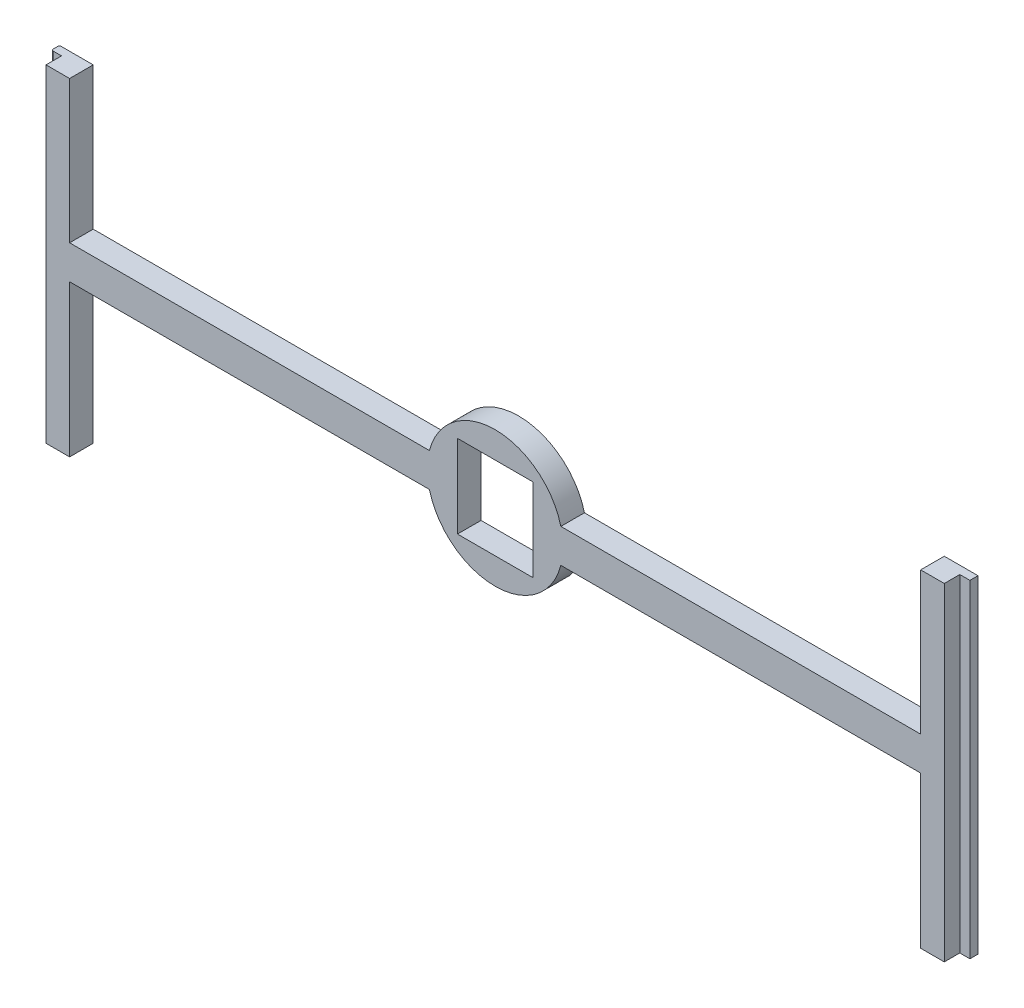
SolidWorks part; units mm, degrees
ref_plane "Front Plane" through (0, 0, 0) normal (0, 0, 1) x (1, 0, 0)
ref_plane "Top Plane" through (0, 0, 0) normal (0, 1, 0) x (1, 0, 0)
ref_plane "Right Plane" through (0, 0, 0) normal (1, 0, 0) x (0, 0, -1)
sketch "Sketch1" plane through (0, 0, 0) normal (0, 0, 1) x (1, 0, 0)
  line L0 (0, 2.5654) -> (0, -2.5654) construction
  line L1 (-63.1, 2.5) -> (-9.7428, 2.5)
  line L3 (-63.1, -2.5) -> (-9.7428, -2.5)
  line L5 (63.1, 25) -> (68.1, 25)
  line L6 (63.1, 25) -> (63.1, 2.5)
  line L7 (63.1, -25) -> (68.1, -25)
  line L8 (68.1, 25) -> (68.1, -25)
  line L9 (-63.1, -25) -> (-68.1, -25)
  line L10 (-68.1, 25) -> (-68.1, -25)
  line L11 (-63.1, 25) -> (-68.1, 25)
  line L12 (-63.1, 25) -> (-63.1, 2.5)
  line L13 (-63.1, -2.5) -> (-63.1, -25)
  line L14 (63.1, -2.5) -> (63.1, -25)
  line L15 (63.1, 2.5) -> (63.1, -2.5) construction
  line L17 (9.7428, 2.5) -> (63.1, 2.5)
  line L18 (9.7428, -2.5) -> (63.1, -2.5)
  circle A5 centre (0, 0) radius 2.54
  arc A6 (-9.7428, -2.5) -> (9.7428, -2.5) centre (0, 0) ccw
  arc A7 (9.7428, 2.5) -> (-9.7428, 2.5) centre (0, 0) ccw
  point P23 (63.1, 0)
  point P24 (0, 0)
  point P25 (-68.1, 0)
  dimension "D5" = 5.08
  dimension "D6" = 20.1168
  dimension "D1" = 126.2
  dimension "D2" = 5
  dimension "D3" = 50
  dimension "D4" = 5
extrude "Boss-Extrude1" add sketch "Sketch1" along normal blind 3.5
sketch "Sketch2" plane through (0, -25, 0) normal (0, -1, 0) x (1, 0, 0)
  line L0 (63.1, 3.5) -> (68.1, 3.5) construction
  line L5 (66.6, 3.5) -> (68.1, 3.5)
  line L6 (66.6, 3.5) -> (66.6, 1.2)
  line L7 (66.6, 1.2) -> (68.1, 1.2)
  line L8 (68.1, 3.5) -> (68.1, 1.2)
  line L9 (68.1, 3.5) -> (68.1, 0) construction
  line L10 (0, 0) -> (0, -12.1014) construction
  line L11 (63.1, 0) -> (68.1, 0) construction
  line L12 (-66.6, 1.2) -> (-68.1, 1.2)
  line L13 (-68.1, 3.5) -> (-68.1, 1.2)
  line L14 (-66.6, 3.5) -> (-66.6, 1.2)
  line L15 (-66.6, 3.5) -> (-68.1, 3.5)
  dimension "D1" = 1.5
  dimension "D2" = 1.2
extrude "Cut-Extrude1" cut sketch "Sketch2" against normal through all
sketch "Sketch3" plane through (0, 0, 3.5) normal (0, 0, 1) x (1, 0, 0)
  line L1 (-5.588, -6.1468) -> (5.588, -6.1468)
  line L2 (-5.588, -6.1468) -> (-5.588, 6.1468)
  line L3 (-5.588, 6.1468) -> (5.588, 6.1468)
  line L4 (5.588, -6.1468) -> (5.588, 6.1468)
  line L5 (-5.588, -6.1468) -> (5.588, 6.1468) construction
  line L6 (-5.588, 6.1468) -> (5.588, -6.1468) construction
  point P0 (0, 0)
  dimension "D1" = 11.176
  dimension "D2" = 12.2936
extrude "Cut-Extrude2" cut sketch "Sketch3" against normal blind 3.81
sketch "Sketch4" plane through (0, 0, 3.5) normal (0, 0, 1) x (1, 0, 0)
  line L0 (-68.1, 25) -> (-68.1, -25) construction
  line L1 (68.1, 25) -> (-68.1, 25)
  line L2 (68.1, 25) -> (68.1, 23.6)
  line L3 (68.1, 23.6) -> (-68.1, 23.6)
  line L4 (-68.1, 25) -> (-68.1, 23.6)
  dimension "D1" = 1.4
extrude "Cut-Extrude3" cut sketch "Sketch4" against normal through all
fillet "Fillet1" radius 0.3 2 edges at (-68.1, -0.7, 0) (-68.1, -0.7, 1.2)
